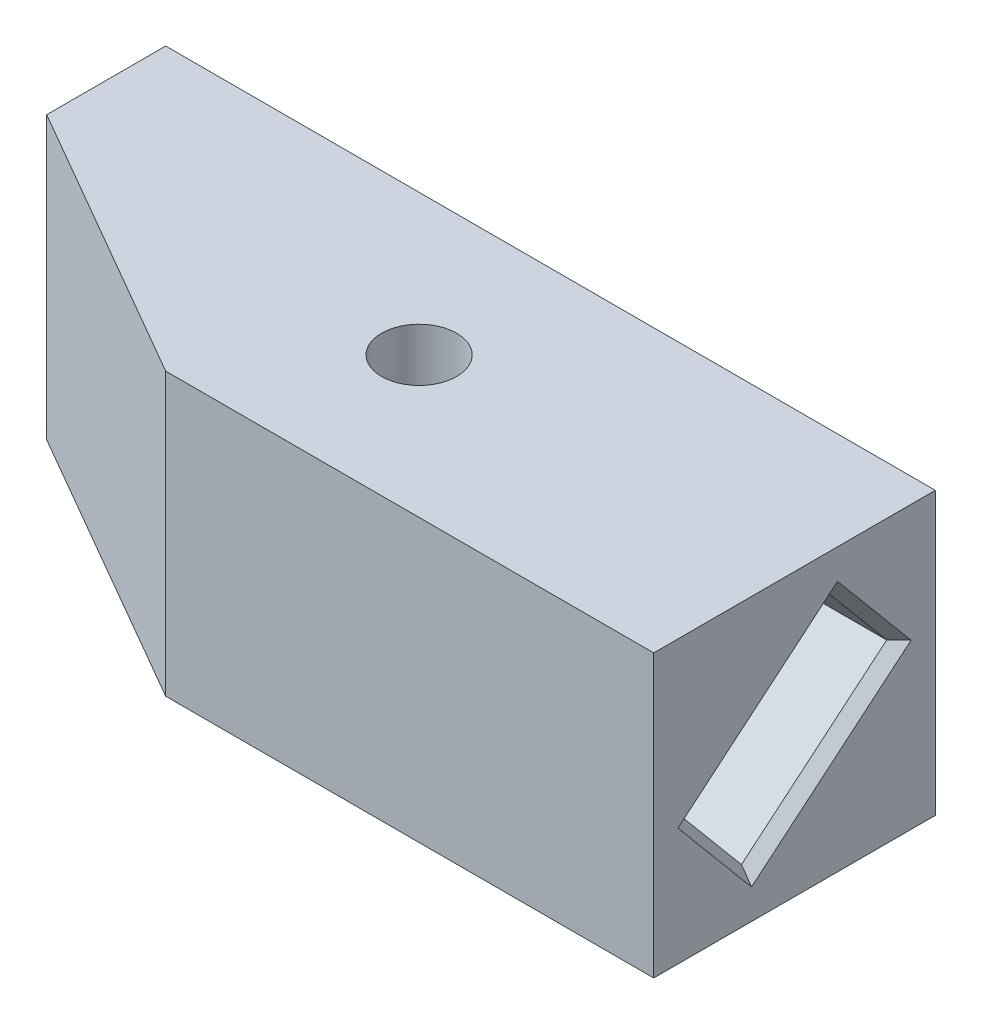
SolidWorks part; units mm, degrees
ref_plane "Спереди" through (0, 0, 0) normal (0, 0, 1) x (1, 0, 0)
ref_plane "Сверху" through (0, 0, 0) normal (0, 1, 0) x (1, 0, 0)
ref_plane "Справа" through (0, 0, 0) normal (1, 0, 0) x (0, 0, -1)
sketch "Эскиз1" plane through (0, 0, 0) normal (0, 1, 0) x (1, 0, 0)
  line L0 (-20, 15) -> (-35, 15)
  line L1 (-20, -15) -> (20, -15)
  line L2 (-35, 15) -> (-35, -15)
  line L3 (-20, 15) -> (20, 15)
  line L4 (20, -15) -> (20, 15)
  line L5 (-20, -15) -> (20, 15) construction
  line L6 (-20, 15) -> (20, -15) construction
  line L7 (-35, -15) -> (-20, -15)
  point P0 (0, 0)
  dimension "D1" = 40
  dimension "D2" = 30
  dimension "D3" = 15
extrude "Бобышка-Вытянуть1" add sketch "Эскиз1" along normal blind 30
sketch "Эскиз2" plane through (0, 30, 0) normal (0, 1, 0) x (1, 0, 0)
  line L0 (-20, -15) -> (-20, 15) construction
  circle A0 centre (-20, 0) radius 4
  dimension "D1" = 15
extrude "Вырез-Вытянуть1" cut sketch "Эскиз2" against normal through all
sketch "Эскиз5" plane through (20, 0, 0) normal (1, 0, 0) x (0, 0, -1)
  line L0 (0, 30) -> (0, 0) construction
  line L1 (-15, 30) -> (15, 0) construction
  line L2 (-15, 0) -> (15, 0) construction
  line L4 (11.0153, 17.5853) -> (4.4588, 25.399)
  line L5 (11.0153, 17.5853) -> (-4.4588, 4.601)
  line L6 (-4.4588, 4.601) -> (-11.0153, 12.4147)
  line L7 (4.4588, 25.399) -> (-11.0153, 12.4147)
  line L8 (11.0153, 17.5853) -> (-11.0153, 12.4147) construction
  line L9 (-4.4588, 4.601) -> (4.4588, 25.399) construction
  point P5 (0, 15)
  point P6 (0, 15)
  dimension "D1" = 20.2
  dimension "D2" = 10.2
  dimension "D3" = 40
extrude "Вырез-Вытянуть4" cut sketch "Эскиз5" against normal blind 30
sketch "Sketch1" plane through (-35, 0, 0) normal (-1, 0, 0) x (0, 0, 1)
  line L0 (0, 30) -> (0, 0) construction
  line L1 (-15, 30) -> (15, 30) construction
  line L2 (-15, 0) -> (15, 0) construction
  line L4 (-15, 0) -> (15, 0)
  line L5 (-15, 0) -> (-15, 30)
  line L6 (-15, 30) -> (15, 30)
  line L7 (15, 0) -> (15, 30)
  line L8 (-15, 0) -> (15, 30) construction
  line L9 (-15, 30) -> (15, 0) construction
  point P6 (0, 15)
extrude "Boss-Extrude1" add sketch "Sketch1" along normal blind 27
chamfer "Chamfer1" distance 30 angle 30 1 edges at (-62, 15, 15)
chamfer "Chamfer2" distance 1 angle 50 4 edges at (20, 8.5078, 7.737) (20, 11.0932, -3.2782) (20, 21.4922, -7.737) (20, 18.9068, 3.2782)
